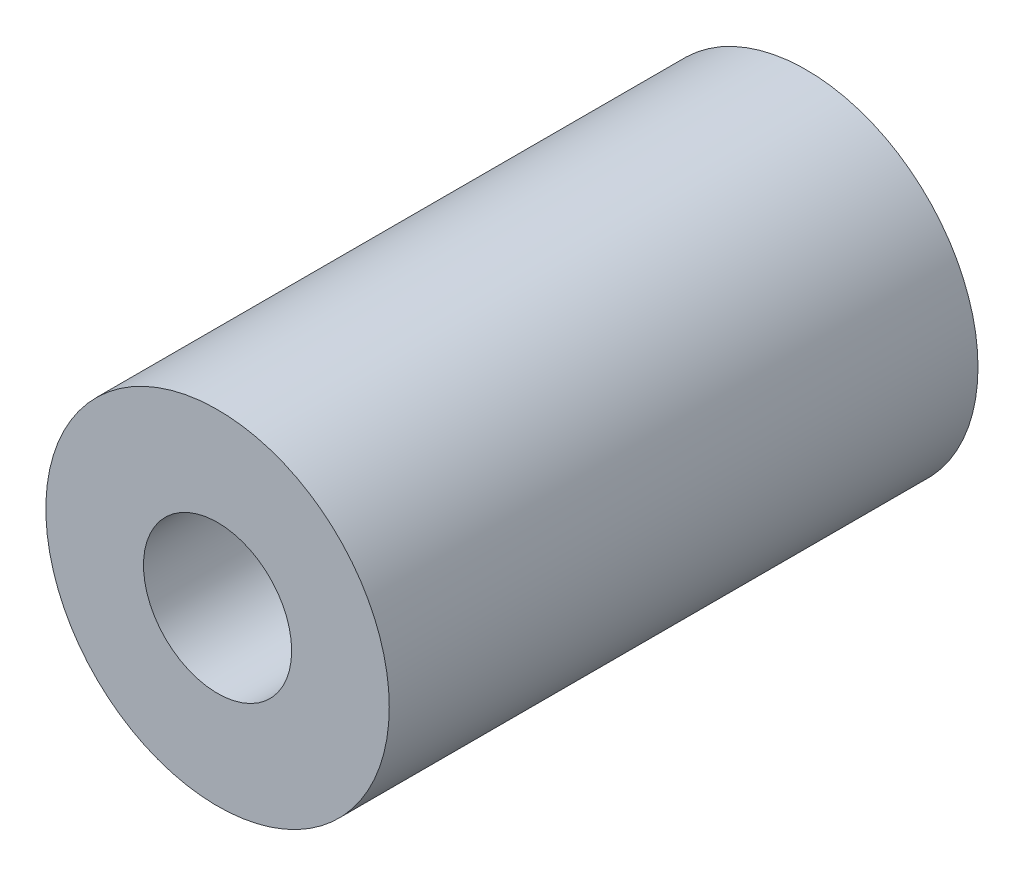
SolidWorks part; units mm, degrees
ref_plane "Plan de face" through (0, 0, 0) normal (0, 0, 1) x (1, 0, 0)
ref_plane "Plan de dessus" through (0, 0, 0) normal (0, 1, 0) x (1, 0, 0)
ref_plane "Plan de droite" through (0, 0, 0) normal (1, 0, 0) x (0, 0, -1)
sketch "Esquisse1" plane through (0, 0, 0) normal (0, 0, 1) x (1, 0, 0)
  circle A0 centre (0, 0) radius 17.5
  dimension "D1" = 35
extrude "Boss.-Extru.1" add sketch "Esquisse1" along normal mid plane 60 contours A0
sketch "Esquisse2" plane through (0, 0, 30) normal (0, 0, 1) x (1, 0, 0)
  circle A0 centre (0, 0) radius 7.55
  dimension "D1" = 15.1
extrude "Enlèv. mat.-Extru.1" cut sketch "Esquisse2" against normal up to surface (30 mm away)
sketch "Esquisse3" plane through (0, 0, -30) normal (0, 0, -1) x (-1, 0, 0)
  circle A0 centre (0, 0) radius 10.05
  dimension "D1" = 20.1
extrude "Enlèv. mat.-Extru.2" cut sketch "Esquisse3" against normal up to surface (30 mm away)
